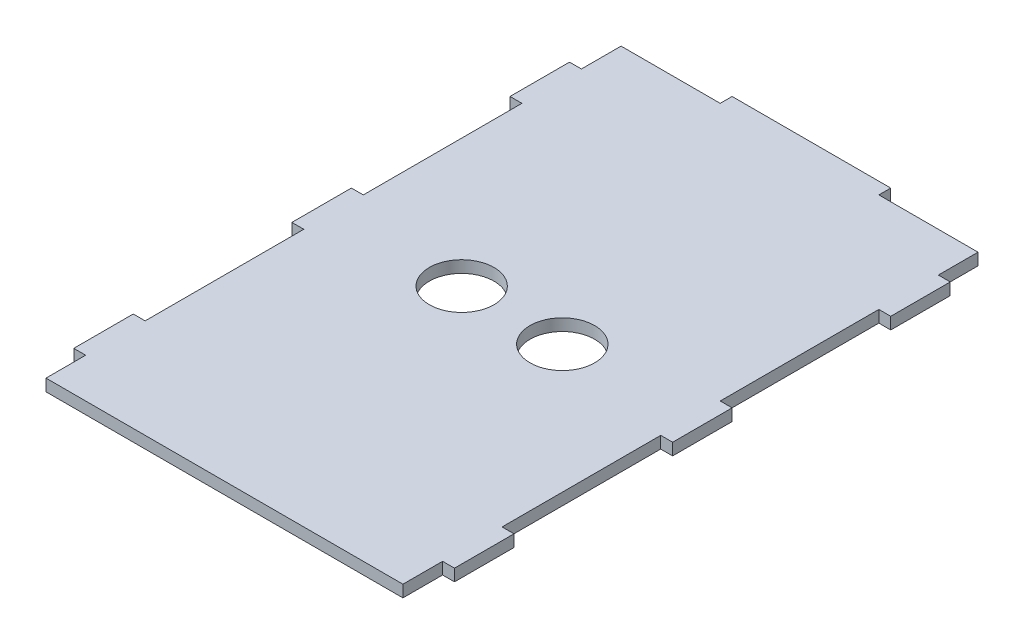
SolidWorks part; units mm, degrees
ref_plane "Front" through (0, 0, 0) normal (0, 0, 1) x (1, 0, 0)
ref_plane "Top" through (0, 0, 0) normal (0, 1, 0) x (1, 0, 0)
ref_plane "Right" through (0, 0, 0) normal (1, 0, 0) x (0, 0, -1)
sketch "Sketch1" plane through (0, 0, 0) normal (0, 1, 0) x (1, 0, 0)
  line L1 (0, 0) -> (90, 0)
  line L2 (0, 0) -> (0, 132)
  line L3 (0, 132) -> (90, 132)
  line L4 (90, 0) -> (90, 132)
  dimension "D1" = 132
  dimension "D2" = 90
extrude "Boss-Extrude1" add sketch "Sketch1" along normal blind 3
sketch "Sketch7" plane through (0, 3, 0) normal (0, 1, 0) x (1, 0, 0)
  line L0 (0, 0) -> (90, 0) construction
  line L1 (0, 145) -> (90, 145)
  line L2 (0, 145) -> (0, 132)
  line L3 (0, 132) -> (90, 132)
  line L4 (90, 145) -> (90, 132)
  line L5 (0, 132) -> (0, 0) construction
  line L6 (90, 0) -> (90, 132) construction
  line L7 (90, 132) -> (0, 132) construction
  dimension "D1" = 145
extrude "Boss-Extrude7" add sketch "Sketch7" against normal blind 3
sketch "Sketch3" [suppressed] plane through (0, 3, 0) normal (0, 1, 0) x (1, 0, 0)
  line L1 (-3, 46) -> (0, 46)
  line L2 (-3, 46) -> (-3, 86)
  line L3 (-3, 86) -> (0, 86)
  line L4 (0, 46) -> (0, 86)
  line L5 (90, 46) -> (93, 46)
  line L6 (90, 46) -> (90, 86)
  line L7 (90, 86) -> (93, 86)
  line L8 (93, 46) -> (93, 86)
  line L9 (90, 0) -> (90, 132) construction
  line L10 (0, 132) -> (0, 0) construction
  point P8 (90, 66)
  point P11 (0, 66)
  dimension "D1" = 3
  dimension "D2" = 3
  dimension "D3" = 40
extrude "Boss-Extrude3" [suppressed] add sketch "Sketch3" against normal through all
sketch "Sketch4" [suppressed] plane through (0, 3, 0) normal (0, 1, 0) x (1, 0, 0)
  line L0 (90, 132) -> (0, 132) construction
  line L1 (20, 152) -> (70, 152)
  line L2 (20, 152) -> (20, 132)
  line L3 (20, 132) -> (70, 132)
  line L4 (70, 152) -> (70, 132)
  point P4 (45, 132)
  point P7 (45, 132)
  dimension "D1" = 50
  dimension "D2" = 20
extrude "Boss-Extrude4" [suppressed] add sketch "Sketch4" against normal blind 3
sketch "Sketch2" plane through (0, 3, 0) normal (0, 1, 0) x (1, 0, 0)
  line L1 (90, 0) -> (0, 0)
  line L2 (90, 0) -> (90, -4)
  line L3 (90, -4) -> (0, -4)
  line L4 (0, 0) -> (0, -4)
  dimension "D1" = 4
extrude "Boss-Extrude2" [suppressed] add sketch "Sketch2" against normal blind 3
sketch "Sketch5" plane through (0, 3, 0) normal (0, 1, 0) x (1, 0, 0)
  line L0 (0, 0) -> (90, 0) construction
  line L1 (-3, 135) -> (0, 135)
  line L2 (-3, 135) -> (-3, 120)
  line L3 (-3, 120) -> (0, 120)
  line L4 (0, 135) -> (0, 120)
  line L5 (-3, 80) -> (0, 80)
  line L6 (-3, 80) -> (-3, 65)
  line L7 (-3, 65) -> (0, 65)
  line L8 (0, 80) -> (0, 65)
  line L9 (-3, 25) -> (0, 25)
  line L10 (-3, 25) -> (-3, 10)
  line L11 (-3, 10) -> (0, 10)
  line L12 (0, 25) -> (0, 10)
  line L13 (90, 135) -> (93, 135)
  line L14 (90, 135) -> (90, 120)
  line L15 (90, 120) -> (93, 120)
  line L16 (93, 135) -> (93, 120)
  line L17 (90, 80) -> (93, 80)
  line L18 (90, 80) -> (90, 65)
  line L19 (90, 65) -> (93, 65)
  line L20 (93, 80) -> (93, 65)
  line L21 (90, 25) -> (93, 25)
  line L22 (90, 25) -> (90, 10)
  line L23 (90, 10) -> (93, 10)
  line L24 (93, 25) -> (93, 10)
  line L25 (-1.5, 0) -> (-1.5, 145) construction
  line L26 (0, 145) -> (0, 0) construction
  line L27 (90, 0) -> (90, 145) construction
  line L30 (90, 145) -> (0, 145) construction
  point P32 (-1.5, 72.5)
  point P33 (-3, 72.5)
  point P36 (-1.5, 10)
  dimension "D1" = 10
  dimension "D2" = 15
  dimension "D3" = 15
  dimension "D4" = 15
  dimension "D5" = 10
  dimension "D6" = 3
  dimension "D7" = 3
extrude "Boss-Extrude5" add sketch "Sketch5" against normal blind 3
sketch "Sketch6" plane through (0, 3, 0) normal (0, 1, 0) x (1, 0, 0)
  line L1 (25, 148) -> (65, 148)
  line L2 (25, 148) -> (25, 145)
  line L3 (25, 145) -> (65, 145)
  line L4 (65, 148) -> (65, 145)
  line L5 (90, 145) -> (0, 145) construction
  point P4 (45, 145)
  point P5 (45, 145)
  point P8 (45, 145)
  dimension "D1" = 40
  dimension "D2" = 3
extrude "Boss-Extrude6" add sketch "Sketch6" against normal blind 3
sketch "Sketch8" plane through (0, 3, 0) normal (0, 1, 0) x (1, 0, 0)
  line L0 (45, 145) -> (45, 0) construction
  line L1 (57.69, 72.5) -> (32.31, 72.5) construction
  line L2 (25, 145) -> (0, 145) construction
  line L3 (65, 148) -> (25, 148) construction
  line L4 (0, 0) -> (90, 0) construction
  circle A0 centre (32.31, 72.5) radius 8.15
  circle A1 centre (57.69, 72.5) radius 8.15
  point P5 (45, 72.5)
  point P11 (45, 148)
  dimension "D1" = 16.3
  dimension "D2" = 16.3
  dimension "D3" = 25.38
extrude "Cut-Extrude1" cut sketch "Sketch8" against normal blind 3
equation "\"D2@Sketch3\"=\"D1@Sketch3\""
equation "\"D3@Sketch5\"=\"D2@Sketch5\""
equation "\"D4@Sketch5\"=\"D2@Sketch5\""
equation "\"D5@Sketch5\"=\"D1@Sketch5\""
equation "\"D7@Sketch5\"=\"D6@Sketch5\""
